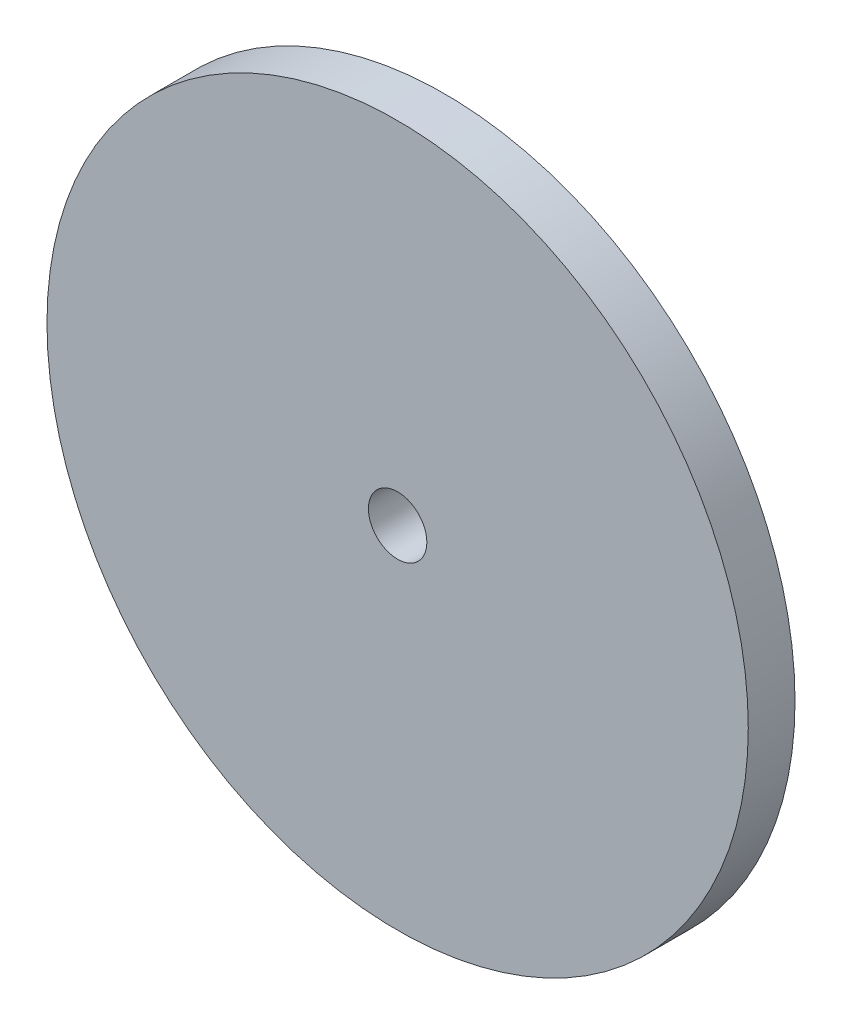
SolidWorks part; units mm, degrees
ref_plane "Front Plane" through (0, 0, 0) normal (0, 0, 1) x (1, 0, 0)
ref_plane "Top Plane" through (0, 0, 0) normal (0, 1, 0) x (1, 0, 0)
ref_plane "Right Plane" through (0, 0, 0) normal (1, 0, 0) x (0, 0, -1)
sketch "Sketch1" plane through (0, 0, 0) normal (0, 0, 1) x (1, 0, 0)
  circle A0 centre (0, 0) radius 30
extrude "Boss-Extrude1" add sketch "Sketch1" along normal blind 4
sketch "Sketch2" plane through (0, 0, 4) normal (0, 0, 1) x (1, 0, 0)
  circle A0 centre (0, 0) radius 2.5
extrude "Cut-Extrude1" cut sketch "Sketch2" against normal blind 4
